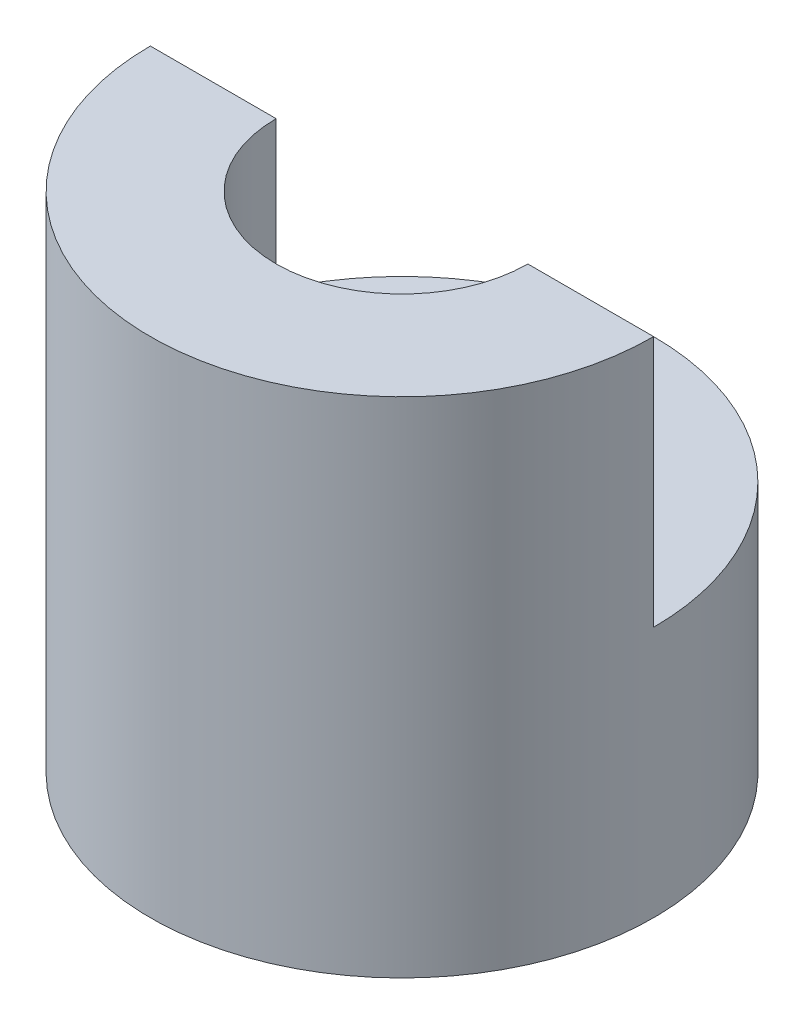
SolidWorks part; units mm, degrees
ref_plane "Front Plane" through (0, 0, 0) normal (0, 0, 1) x (1, 0, 0)
ref_plane "Top Plane" through (0, 0, 0) normal (0, 1, 0) x (1, 0, 0)
ref_plane "Right Plane" through (0, 0, 0) normal (1, 0, 0) x (0, 0, -1)
sketch "Sketch1" plane through (0, 0, 0) normal (0, 0, 1) x (1, 0, 0)
  line L1 (0, 0) -> (10, 0)
  line L2 (0, 0) -> (0, 20)
  line L3 (0, 20) -> (10, 20)
  line L4 (10, 0) -> (10, 20)
  dimension "D1" = 20
  dimension "D2" = 10
revolve "Revolve1" add sketch "Sketch1" angle 360 about L2
sketch "Sketch2" plane through (0, 20, 0) normal (0, 1, 0) x (1, 0, 0)
  circle A0 centre (0, 0) radius 5
  dimension "D1" = 10
extrude "Cut-Extrude1" cut sketch "Sketch2" against normal blind 20
sketch "Sketch3" plane through (0, 20, 0) normal (0, 1, 0) x (1, 0, 0)
  line L0 (-10, 0) -> (-5, 0)
  line L1 (5, 0) -> (10, 0)
  arc A0 (10, 0) -> (-10, 0) centre (0, 0) ccw
  circle A1 centre (0, 0) radius 10 construction
  arc A2 (-5, 0) -> (5, 0) centre (0, 0) cw
  circle A3 centre (0, 0) radius 5 construction
  dimension "D3" = 5
  dimension "D4" = 10
  dimension "D1" = 5
  dimension "D2" = 5
extrude "Cut-Extrude2" cut sketch "Sketch3" against normal blind 10
